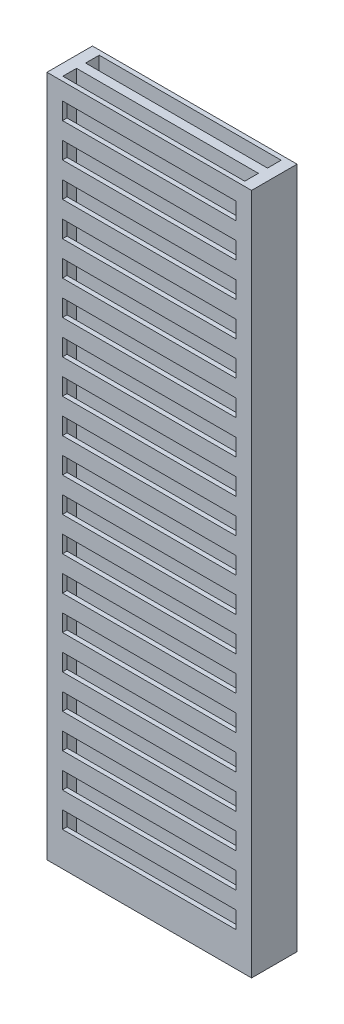
SolidWorks part; units mm, degrees
ref_plane "Front Plane" through (0, 0, 0) normal (0, 0, 1) x (1, 0, 0)
ref_plane "Top Plane" through (0, 0, 0) normal (0, 1, 0) x (1, 0, 0)
ref_plane "Right Plane" through (0, 0, 0) normal (1, 0, 0) x (0, 0, -1)
sketch "Sketch1" plane through (0, 0, 0) normal (0, 1, 0) x (1, 0, 0)
  line L1 (-4.5, -1) -> (4.5, -1)
  line L2 (-4.5, -1) -> (-4.5, 1)
  line L3 (-4.5, 1) -> (4.5, 1)
  line L4 (4.5, -1) -> (4.5, 1)
  line L5 (-4.5, -1) -> (4.5, 1) construction
  line L6 (-4.5, 1) -> (4.5, -1) construction
  point P0 (0, 0)
  dimension "D1" = 9
  dimension "D2" = 2
extrude "Boss-Extrude1" add sketch "Sketch1" along normal mid plane 30
sketch "Sketch2" plane through (0, 15, 0) normal (0, 1, 0) x (1, 0, 0)
  line L1 (-4, 0.2) -> (4, 0.2)
  line L2 (-4, 0.2) -> (-4, 0.8)
  line L3 (-4, 0.8) -> (4, 0.8)
  line L4 (4, 0.2) -> (4, 0.8)
  line L5 (-4, 0.2) -> (4, 0.8) construction
  line L6 (-4, 0.8) -> (4, 0.2) construction
  point P0 (0, 0.5)
  dimension "D1" = 0.6
  dimension "D2" = 8
  dimension "D3" = 0
  dimension "D4" = 0.5
extrude "Cut-Extrude1" cut sketch "Sketch2" against normal through all and the other way through all
mirror "Mirror1" about plane through (0, 0, 0) normal (0, 0, 1) of "Cut-Extrude1"
sketch "Sketch3" plane through (0, 0, 1) normal (0, 0, 1) x (1, 0, 0)
  line L0 (0, -1.1) -> (0, 1.1) construction
  line L1 (-3.8171, 13.5) -> (3.8171, 13.5)
  line L2 (-3.8171, 13.5) -> (-3.8171, 14.25)
  line L3 (-3.8171, 14.25) -> (3.8171, 14.25)
  line L4 (3.8171, 13.5) -> (3.8171, 14.25)
  line L5 (-3.8171, 13.5) -> (3.8171, 14.25) construction
  line L6 (-3.8171, 14.25) -> (3.8171, 13.5) construction
  line L7 (-4.5, 15) -> (4.5, 15) construction
  point P0 (0, 13.875)
  dimension "D1" = 0.75
  dimension "D2" = 0.75
extrude "Cut-Extrude2" cut sketch "Sketch3" against normal up to next (0.2 mm away)
pattern_linear "LPattern1" count 19 spacing 1.5 along (0, -1, 0) of "Cut-Extrude2"
mirror "Mirror2" about plane through (0, 0, 0) normal (0, 0, 1) of "LPattern1", "Cut-Extrude2"
